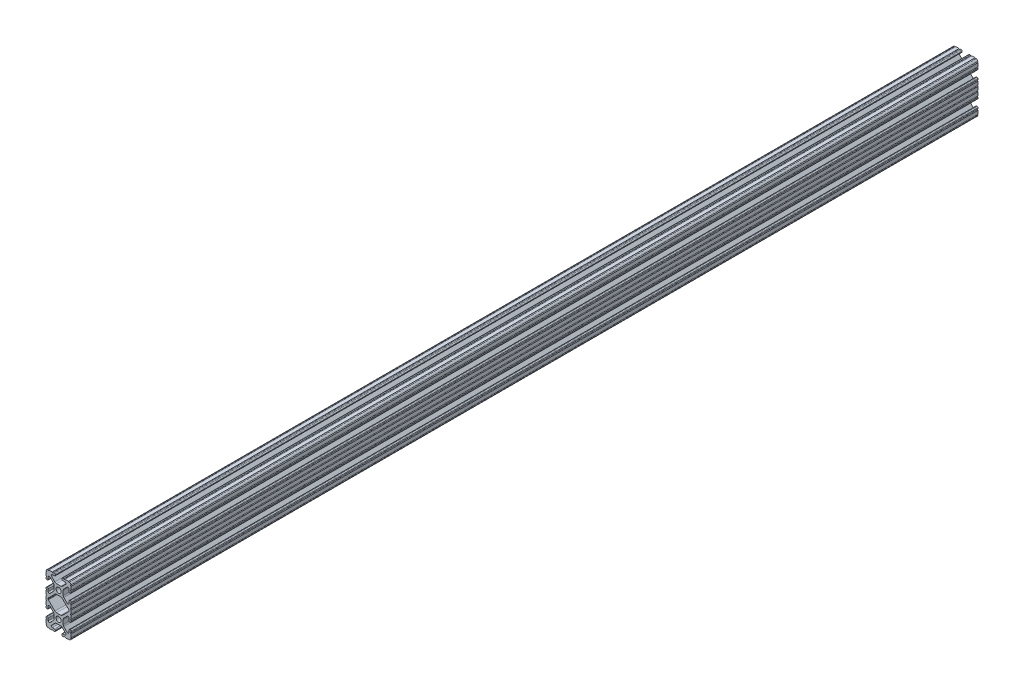
SolidWorks part; units mm, degrees
ref_plane "Front Plane" through (0, 0, 0) normal (0, 0, 1) x (1, 0, 0)
ref_plane "Top Plane" through (0, 0, 0) normal (0, 1, 0) x (1, 0, 0)
ref_plane "Right Plane" through (0, 0, 0) normal (1, 0, 0) x (0, 0, -1)
sketch "Sketch2" plane through (0, 0, 0) normal (0, 0, 1) x (1, 0, 0)
  line L0 (0, 25.4) -> (0, -25.4) construction
  line L1 (-12.7, 0) -> (12.7, 0) construction
  line L2 (3.2512, -25.4) -> (12.7, -25.4)
  line L3 (12.7, -25.4) -> (12.7, -15.9512)
  line L4 (3.2512, -25.4) -> (3.2512, -23.1902)
  line L5 (3.2512, -23.1902) -> (8.9276, -23.1902)
  line L6 (8.9276, -23.1902) -> (3.0856, -17.3482)
  line L7 (0, -12.7) -> (12.7, -25.4) construction
  line L8 (12.7, -15.9512) -> (10.4902, -15.9512)
  line L9 (10.4902, -15.9512) -> (10.4902, -21.6276)
  line L10 (10.4902, -21.6276) -> (4.6482, -15.7856)
  circle A0 centre (0, -12.7) radius 2.6035
  arc A1 (6.3485, -23.1902) -> (7.1039, -21.3665) centre (6.3485, -22.1219) ccw construction
  point P8 (0, -17.3482)
  dimension "Center Hole Diameter" = 5.207
  dimension "Rail Height" = 50.8
  dimension "Rail Width" = 25.4
  dimension "T-Slot Width" = 6.5024
  dimension "Slot Inner Width" = 14.8336
  dimension "Thickness" = 2.2098
  dimension "Slot Depth" = 5.842
  dimension "D1" = 2.2098
  dimension "C to C" = 25.4
sketch "Sketch3" plane through (0, 0, 0) normal (1, 0, 0) x (0, 0, -1)
  line L0 (-457.2, -25.4) -> (457.2, -25.4) construction
  line L1 (-431.8, 0) -> (431.8, 0) construction
  dimension "Length" = 914.4
  dimension "D1" = 25.4
sketch "Sketch4" plane through (0, 0, 0) normal (0, 0, 1) x (1, 0, 0)
  line L0 (4.1904, -25.4) -> (10.1173, -25.4)
  line L1 (3.2512, -25.4) -> (12.7, -25.4) construction
  line L2 (3.2512, -25.4) -> (3.2512, -23.1902) construction
  line L3 (3.2512, -23.1902) -> (8.9276, -23.1902) construction
  line L4 (3.2512, -24.1294) -> (3.2512, -24.4608)
  line L5 (4.1904, -23.1902) -> (6.3485, -23.1902)
  line L6 (0, -17.3482) -> (2.164, -17.3482)
  line L7 (8.9276, -23.1902) -> (3.0856, -17.3482) construction
  line L8 (3.7373, -17.9999) -> (7.1039, -21.3665)
  line L9 (12.7, -25.4) -> (12.7, -15.9512) construction
  line L10 (10.4902, -21.6276) -> (4.6482, -15.7856) construction
  line L11 (10.4902, -15.9512) -> (10.4902, -21.6276) construction
  line L12 (10.4902, -19.0485) -> (10.4902, -16.8904)
  line L13 (12.7, -15.9512) -> (10.4902, -15.9512) construction
  line L14 (11.4294, -15.9512) -> (11.7608, -15.9512)
  line L15 (12.7, -16.8904) -> (12.7, -22.8173)
  line L16 (8.6665, -19.8039) -> (5.2999, -16.4373)
  line L17 (4.6482, -12.7) -> (4.6482, -14.864)
  line L19 (0, -17.3482) -> (0, -15.3035)
  line L20 (0, 25.4) -> (0, -25.4) construction
  line L21 (4.6482, -12.7) -> (2.6035, -12.7)
  arc A0 (3.2512, -24.4608) -> (4.1904, -25.4) centre (4.1904, -24.4608) ccw
  circle A1 centre (0, -12.7) radius 2.6035 construction
  arc A2 (3.2512, -24.1294) -> (4.1904, -23.1902) centre (4.1904, -24.1294) cw
  arc A3 (6.3485, -23.1902) -> (7.1039, -21.3665) centre (6.3485, -22.1219) ccw
  arc A4 (2.164, -17.3482) -> (3.7373, -17.9999) centre (2.164, -19.5732) cw
  arc A5 (10.1173, -25.4) -> (12.7, -22.8173) centre (10.1173, -22.8173) ccw
  arc A6 (8.6665, -19.8039) -> (10.4902, -19.0485) centre (9.4219, -19.0485) ccw
  arc A7 (10.4902, -16.8904) -> (11.4294, -15.9512) centre (11.4294, -16.8904) cw
  arc A8 (11.7608, -15.9512) -> (12.7, -16.8904) centre (11.7608, -16.8904) cw
  arc A9 (5.2999, -16.4373) -> (4.6482, -14.864) centre (6.8732, -14.864) cw
  arc A11 (0, -15.3035) -> (2.6035, -12.7) centre (0, -12.7) ccw
  dimension "D1" = 2.5827
  dimension "D2" = 2.225
  dimension "D3" = 0.9392
extrude "Boss-Extrude1" add sketch "Sketch4" along normal mid plane 914.4
sketch "Sketch5" plane through (0, 0, 0) normal (0, 0, 1) x (1, 0, 0)
  line L0 (3.2512, -25.4) -> (12.7, -25.4) construction
  line L1 (4.1904, -23.1902) -> (6.3485, -23.1902) construction
  line L3 (0, -12.7) -> (12.7, -25.4) construction
  line L4 (6.3485, -23.1902) -> (6.3485, -25.4) construction
  line L5 (8.9276, -23.1902) -> (3.0856, -17.3482) construction
  circle A0 centre (10.3562, -25.4) radius 0.5524
  circle A1 centre (5.796, -25.4) radius 0.5524
  circle A2 centre (12.7, -23.0562) radius 0.5524
  circle A3 centre (12.7, -18.496) radius 0.5524
  point P10 (5.2694, -23.1902)
  point P12 (9.4219, -19.0485)
  dimension "D1" = 1.1049
extrude "Cut-Extrude1" cut sketch "Sketch5" against normal through all both and the other way through all
mirror "Mirror1" about plane through (4.6482, -12.7, 457.2) normal (0, -1, 0) of bodies 137 134
sketch "Sketch6" plane through (0, 0, 0) normal (0, 0, 1) x (1, 0, 0)
  line L0 (12.7, -1.7914) -> (12.7, 0)
  line L1 (12.7, 0) -> (9.8037, 0)
  line L2 (-12.7, 0) -> (12.7, 0) construction
  line L3 (9.8037, 0) -> (9.8037, -2.3438)
  line L4 (9.8037, -2.3438) -> (12.1476, -2.3438)
  circle A0 centre (12.7, -2.3438) radius 0.5524 construction
  arc A1 (12.7, -1.7914) -> (12.1476, -2.3438) centre (12.7, -2.3438) ccw
  arc A4 (12.58, -1.8046) -> (12.7, -2.8963) centre (12.7, -2.3438) ccw construction
  arc A6 (9.8037, 0) -> (10.8954, -0.12) centre (10.3562, 0) ccw construction
extrude "Boss-Extrude2" add sketch "Sketch6" along normal mid plane 914.4
sketch "Sketch7" plane through (0, 0, 0) normal (0, 0, 1) x (1, 0, 0)
  line L0 (5.4206, -5.7168) -> (10.3284, -0.809)
  line L1 (3.7373, -7.4001) -> (7.1039, -4.0335) construction
  line L2 (10.4902, -0.4184) -> (10.4902, 0)
  line L3 (0, 0) -> (10.4902, 0)
  line L4 (-12.7, 0) -> (12.7, 0) construction
  line L5 (0, 0) -> (5.4206, -5.7168)
  arc A0 (10.3284, -0.809) -> (10.4902, -0.4184) centre (9.9377, -0.4184) ccw
  arc A3 (12.7, -1.7914) -> (12.7, -2.8963) centre (12.7, -2.3438) ccw construction
extrude "Cut-Extrude2" cut sketch "Sketch7" against normal through all both and the other way through all
mirror "Mirror2" about plane through (0, 0, 0) normal (0, 1, 0) of bodies 139 135
mirror "Mirror3" about plane through (0, 0, 0) normal (1, 0, 0) of bodies 136
equation "\"D1@Boss-Extrude1\"=\"Length@Sketch3\""
equation "\"D1@Sketch2\"=\"Thickness@Sketch2\""
equation "\"D2@Sketch4\"=\"Slot Inner Width@Sketch2\"*0.15"
equation "\"D1@Sketch4\"=\"D3@Sketch4\"*2.75"
equation "\"D3@Sketch4\"=\"Thickness@Sketch2\"*0.425"
equation "\"D1@Sketch5\"=\"Thickness@Sketch2\"*0.5"
equation "\"D1@Boss-Extrude2\"=\"Length@Sketch3\""
